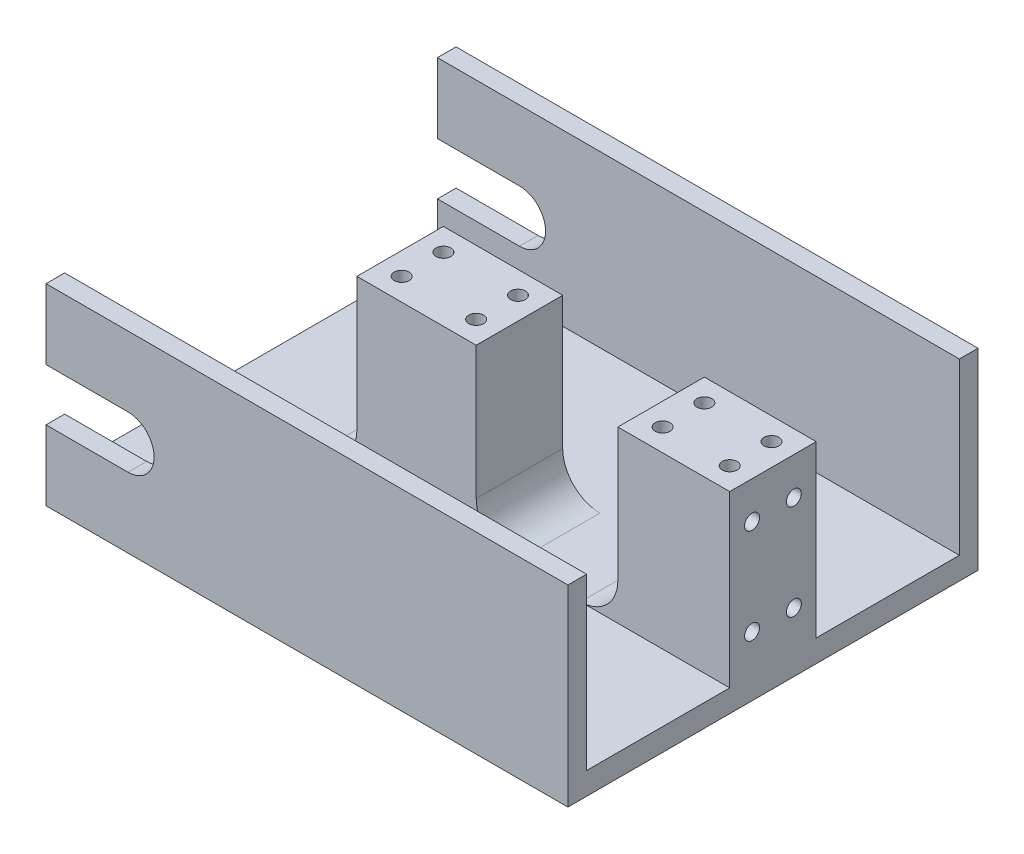
SolidWorks part; units mm, degrees
ref_plane "Front" through (0, 0, 0) normal (0, 0, 1) x (1, 0, 0)
ref_plane "Top" through (0, 0, 0) normal (0, 1, 0) x (1, 0, 0)
ref_plane "Right" through (0, 0, 0) normal (1, 0, 0) x (0, 0, -1)
sketch "Sketch1" plane through (0, 0, 0) normal (0, 0, 1) x (1, 0, 0)
  line L1 (-35, 1.5) -> (35, 1.5)
  line L2 (-35, 1.5) -> (-35, -1.5)
  line L3 (-35, -1.5) -> (35, -1.5)
  line L4 (35, 1.5) -> (35, -1.5)
  line L5 (-35, 1.5) -> (35, -1.5) construction
  line L6 (-35, -1.5) -> (35, 1.5) construction
  point P0 (0, 0)
  dimension "D1" = 70
  dimension "D2" = 3
extrude "Boss-Extrude1" add sketch "Sketch1" along normal blind 55
sketch "Sketch2" plane through (0, 1.5, 0) normal (0, 1, 0) x (1, 0, 0)
  line L0 (35, -55) -> (35, 0) construction
  line L1 (-35, 0) -> (35, 0)
  line L2 (-35, 0) -> (-35, -2.5)
  line L3 (-35, -2.5) -> (35, -2.5)
  line L4 (35, 0) -> (35, -2.5)
  line L7 (35, -55) -> (35, -52.5)
  line L8 (-35, -52.5) -> (35, -52.5)
  line L9 (-35, -55) -> (-35, -52.5)
  line L10 (-35, -55) -> (35, -55)
  dimension "D1" = 2.5
extrude "Boss-Extrude2" add sketch "Sketch2" along normal blind 22.8
sketch "Sketch5" plane through (0, 0, 55) normal (0, 0, 1) x (1, 0, 0)
  line L1 (-35, 24.3) -> (-35, -1.5) construction
  circle A0 centre (-24, 11.4) radius 3.5
  point P5 (-35, 11.4)
  dimension "D1" = 7
  dimension "D2" = 11
extrude "Cut-Extrude1" cut sketch "Sketch5" against normal blind 84.8
sketch "Sketch6" plane through (0, 24.3, 0) normal (0, 1, 0) x (1, 0, 0)
  line L0 (-35, -2.5) -> (35, -2.5) construction
  line L1 (-15, -21.7) -> (1, -21.7)
  line L2 (-15, -21.7) -> (-15, -33.3)
  line L3 (-15, -33.3) -> (1, -33.3)
  line L4 (1, -21.7) -> (1, -33.3)
  line L5 (35, -52.5) -> (-35, -52.5) construction
  line L6 (-35, -52.5) -> (-35, -2.5) construction
  line L7 (35, -52.5) -> (35, -2.5) construction
  line L8 (35, -21.7) -> (20, -21.7)
  line L9 (35, -21.7) -> (35, -33.3)
  line L10 (35, -33.3) -> (20, -33.3)
  line L11 (20, -21.7) -> (20, -33.3)
  dimension "D1" = 19.2
  dimension "D2" = 19.2
  dimension "D3" = 20
  dimension "D4" = 36
  dimension "D5" = 15
extrude "Boss-Extrude7" add sketch "Sketch6" against normal up to surface (22.8 mm away) up to face at (0, 1.5, 27.5)
sketch "Sketch7" plane through (0, 24.3, 0) normal (0, 1, 0) x (1, 0, 0)
  line L0 (1, -21.7) -> (-15, -21.7) construction
  line L1 (-15, -21.7) -> (-15, -33.3) construction
  line L2 (1, -33.3) -> (1, -21.7) construction
  line L3 (-15, -33.3) -> (1, -33.3) construction
  line L4 (35, -21.7) -> (20, -21.7) construction
  line L5 (20, -21.7) -> (20, -33.3) construction
  line L6 (35, -21.7) -> (20, -21.7) construction
  line L7 (35, -33.3) -> (35, -21.7) construction
  line L8 (20, -33.3) -> (35, -33.3) construction
  line L9 (20, -21.7) -> (20, -33.3) construction
  circle A0 centre (-12, -24.7) radius 1
  circle A1 centre (23, -30.3) radius 1
  circle A2 centre (-2, -24.7) radius 1
  circle A3 centre (-2, -30.3) radius 1
  circle A4 centre (-12, -30.3) radius 1
  circle A5 centre (23, -24.7) radius 1
  circle A6 centre (32, -24.7) radius 1
  circle A7 centre (32, -30.3) radius 1
  dimension "D1" = 2
  dimension "D2" = 2
  dimension "D3" = 3
  dimension "D4" = 3
  dimension "D5" = 3
  dimension "D6" = 3
  dimension "D7" = 3
  dimension "D8" = 3
  dimension "D9" = 3
  dimension "D10" = 3
  dimension "D11" = 3
  dimension "D12" = 3
  dimension "D13" = 3
  dimension "D14" = 3
  dimension "D15" = 3
  dimension "D16" = 3
  dimension "D17" = 3
  dimension "D18" = 3
extrude "Cut-Extrude2" cut sketch "Sketch7" against normal blind 8
sketch "Sketch8" plane through (35, 0, 0) normal (1, 0, 0) x (0, 0, -1)
  line L0 (-33.3, 1.5) -> (-33.3, 24.3) construction
  line L1 (-33.3, 24.3) -> (-21.7, 24.3) construction
  line L2 (-52.5, 1.5) -> (-33.3, 1.5) construction
  line L3 (-27.5, 24.3) -> (-27.5, 29.6427)
  circle A0 centre (-30.3, 19.3) radius 1
  circle A1 centre (-30.3, 6.5) radius 1
  circle A2 centre (-24.7, 6.5) radius 1
  circle A3 centre (-24.7, 19.3) radius 1
  dimension "D1" = 2
  dimension "D2" = 2
  dimension "D3" = 3
  dimension "D4" = 3
  dimension "D5" = 5
  dimension "D6" = 5
extrude "Cut-Extrude3" cut sketch "Sketch8" against normal blind 8 contours A3 | A0 | A2 | A1
fillet "Fillet1" radius 5 3 edges at (-15, 1.5, 27.5) (1, 1.5, 27.5) (20, 1.5, 27.5)
sketch "Sketch9" plane through (0, 0, 55) normal (0, 0, 1) x (1, 0, 0)
  line L1 (-24, 14.9) -> (-38.0844, 14.9)
  line L2 (-24, 14.9) -> (-24, 7.9)
  line L3 (-24, 7.9) -> (-38.0844, 7.9)
  line L4 (-38.0844, 14.9) -> (-38.0844, 7.9)
  circle A0 centre (-24, 11.4) radius 3.5 construction
extrude "Cut-Extrude4" cut sketch "Sketch9" against normal blind 66
